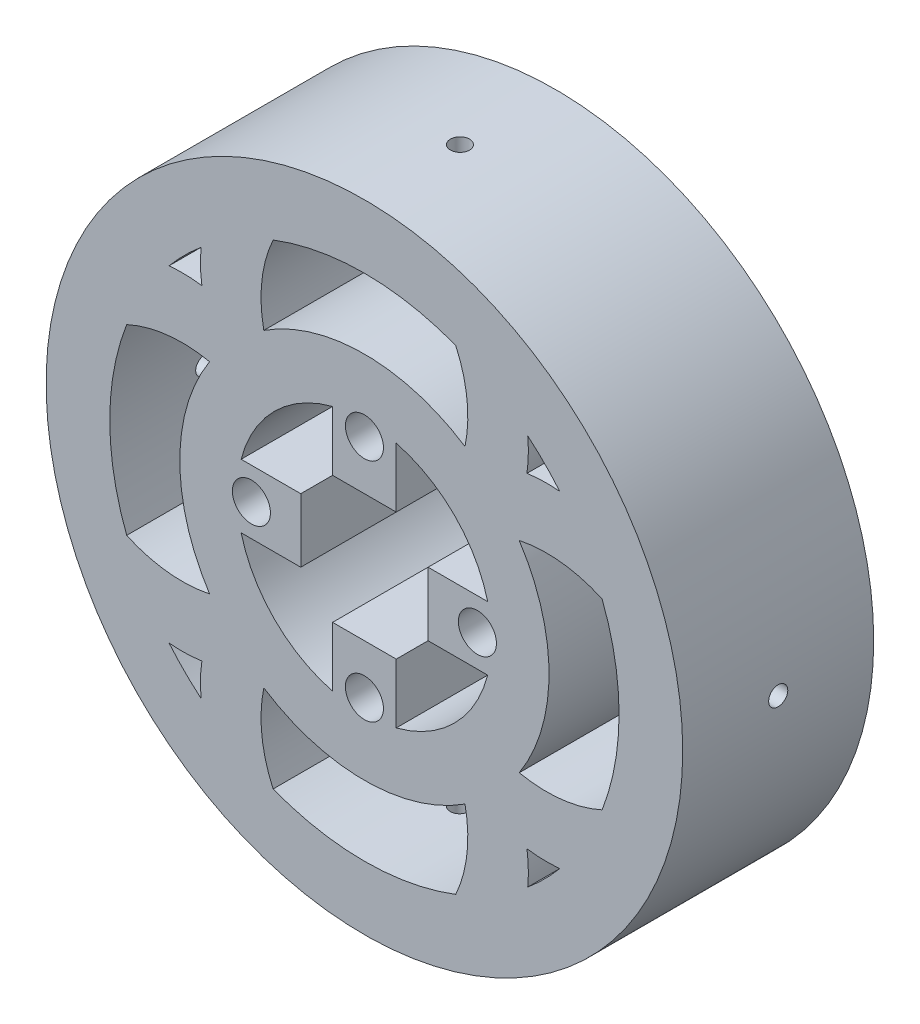
SolidWorks part; units mm, degrees
ref_plane "Front Plane" through (0, 0, 0) normal (0, 0, 1) x (1, 0, 0)
ref_plane "Top Plane" through (0, 0, 0) normal (0, 1, 0) x (1, 0, 0)
ref_plane "Right Plane" through (0, 0, 0) normal (1, 0, 0) x (0, 0, -1)
sketch "Sketch6" plane through (0, 0, 0) normal (0, 0, 1) x (1, 0, 0)
  circle A0 centre (0, 0) radius 20
  circle A1 centre (0, 0) radius 29
  dimension "D1" = 40
  dimension "D2" = 58
extrude "Inner Ring" add sketch "Sketch6" against normal blind 30 separate body
sketch "Sketch7" plane through (0, 0, 0) normal (0, 0, 1) x (1, 0, 0)
  line L2 (-10, 5) -> (-10, -5)
  line L3 (-5, 10) -> (5, 10)
  line L4 (10, 5) -> (10, -5)
  line L5 (-5, -10) -> (5, -10)
  line L14 (-19.3649, 5) -> (-10, 5)
  line L15 (-19.3649, -5) -> (-10, -5)
  line L16 (-5, 19.3649) -> (-5, 10)
  line L17 (5, 19.3649) -> (5, 10)
  line L18 (19.3649, 5) -> (10, 5)
  line L19 (19.3649, -5) -> (10, -5)
  line L20 (5, -19.3649) -> (5, -10)
  line L21 (-5, -19.3649) -> (-5, -10)
  circle A1 centre (0, 0) radius 20
  circle M19 centre (0, 0) radius 20
  dimension "D1" = 20
  dimension "D2" = 20
  dimension "D3" = 10
  dimension "D5" = 10
  dimension "D7" = 10
  dimension "D8" = 10
extrude "Motor Connector Cut" add sketch "Sketch7" against normal blind 30 contours L19 L18 L4 M19 | L17 L16 L3 M19 | L15 L2 L14 M19 | L21 L20 L5 M19
sketch "Sketch8" plane through (0, 0, 0) normal (0, 0, 1) x (1, 0, 0)
  circle A1 centre (0, 17.75) radius 2.987
  circle A2 centre (17.75, 0) radius 2.987
  circle A3 centre (0, -17.75) radius 2.987
  circle A4 centre (-17.75, 0) radius 2.987
  dimension "D1" = 5.974
  dimension "D2" = 5.974
  dimension "D3" = 5.974
  dimension "0.0049m" = 5.974
sketch "Sketch9" plane through (0, 0, 0) normal (0, 0, 1) x (1, 0, 0)
  circle A0 centre (0, 0) radius 50
  circle A18 centre (0, 0) radius 29
  dimension "D2" = 100
extrude "Outside Ring Extrusion" add sketch "Sketch9" against normal blind 30
sketch "Sketch12" plane through (0, 0, 0) normal (0, 0, 1) x (1, 0, 0)
  circle A0 centre (0, 0) radius 27.5
  circle A1 centre (0, 0) radius 45
  dimension "D1" = 55
  dimension "D2" = 90
extrude "Cut-Extrude6" cut sketch "Sketch12" against normal blind 56 and the other way blind 38
extrude "Motor Connector Holes" cut sketch "Sketch8" against normal blind 41 and the other way blind 27
sketch "Sketch10" plane through (0, 0, 0) normal (0, 0, 1) x (1, 0, 0)
  circle A0 centre (0, 0) radius 29
  arc A4 (-24.0947, 20.4191) -> (-41.6064, 16.7952) centre (-29, 0) ccw
  circle A5 centre (0, 0) radius 50
  arc A6 (-0.0957, 0) -> (0, 0.0957) centre (-17.7016, 17.7016) ccw
  arc A9 (-28.6072, 4.7568) -> (-42.4805, -14.6492) centre (-17.7016, -17.7016) ccw
  arc A10 (-20.4191, 24.0947) -> (-38.2638, 23.4049) centre (-28.6072, 4.7568) ccw
  arc A11 (-24.3176, 15.8004) -> (-43.8179, 9.722) centre (-28.6072, -4.7568) ccw
  circle A18 centre (0, 0) radius 29
  arc A19 (14.3758, 42.4453) -> (-4.7568, 28.6072) centre (17.7016, 17.7016) ccw
  circle A20 centre (0, -0.0957) radius 44.9043
  arc A21 (24.3176, -15.8004) -> (43.8731, -9.6638) centre (28.6072, 4.7568) ccw
  arc A22 (43.8179, 9.722) -> (24.3176, 15.8004) centre (28.6072, -4.7568) ccw
  arc A23 (41.6064, 16.7952) -> (21.3966, 19.5752) centre (29, 0) ccw
  arc A24 (49.5968, 4.0954) -> (49.3228, 8.2014) centre (28.6072, 4.7568) ccw
  arc A25 (49.5968, -4.0954) -> (49.5968, 4.0954) centre (29, 0) ccw
  arc A26 (28.6072, -4.7568) -> (42.4628, 14.5092) centre (17.7016, 17.7016) ccw
  arc A27 (42.4805, -14.6492) -> (28.6072, 4.7568) centre (17.7016, -17.7016) ccw
  arc A28 (49.3228, -8.2014) -> (49.5968, -4.0954) centre (28.6072, -4.7568) ccw
  arc A29 (25.5301, 25.5301) -> (23.4328, 38.2096) centre (4.7568, 28.6072) ccw
  arc A30 (23.2856, -38.4907) -> (22.8197, -17.8959) centre (4.7568, -28.6072) ccw
  arc A31 (20.4191, 24.0947) -> (16.8561, 41.5248) centre (0, 29) ccw
  arc A32 (24.0947, -20.4191) -> (41.717, -16.7116) centre (29, 0) ccw
  arc A33 (15.8004, 24.3176) -> (9.8231, 43.721) centre (-4.7568, 28.6072) ccw
  arc A34 (4.7568, 28.6072) -> (-14.3758, 42.4453) centre (-17.7016, 17.7016) ccw
  arc A35 (16.6483, -41.7998) -> (20.4191, -24.0947) centre (0, -29) ccw
  arc A36 (9.5599, -43.9706) -> (15.8004, -24.3176) centre (-4.7568, -28.6072) ccw
  arc A38 (17.8959, -22.8197) -> (38.435, -23.3152) centre (28.6072, -4.7568) ccw
  arc A39 (-14.7836, -42.4967) -> (4.7568, -28.6072) centre (-17.7016, -17.7016) ccw
  arc A40 (-38.435, -23.3152) -> (-20.4191, -24.0947) centre (-28.6072, -4.7568) ccw
  arc A41 (-43.8731, -9.6638) -> (-24.3176, -15.8004) centre (-28.6072, 4.7568) ccw
  arc A43 (-41.717, -16.7116) -> (-21.3966, -19.5752) centre (-29, 0) ccw
  arc A44 (0, -0.0957) -> (-0.0957, 0) centre (-17.7016, -17.7016) ccw
  arc A45 (-42.4628, 14.5092) -> (-28.6072, -4.7568) centre (-17.7016, 17.7016) ccw
  arc A46 (-4.7568, -28.6072) -> (14.7836, -42.4967) centre (17.7016, -17.7016) ccw
  arc A47 (-23.4328, 38.2096) -> (-24.0947, 20.4191) centre (-4.7568, 28.6072) ccw
  arc A48 (-15.8004, -24.3176) -> (-9.5599, -43.9706) centre (4.7568, -28.6072) ccw
  arc A49 (-16.8561, 41.5248) -> (-19.5752, 21.3966) centre (0, 29) ccw
  arc A50 (-20.4191, -24.0947) -> (-16.6483, -41.7998) centre (0, -29) ccw
  arc A51 (-9.8231, 43.721) -> (-15.8004, 24.3176) centre (4.7568, 28.6072) ccw
  arc A52 (-25.5301, -25.5301) -> (-23.2856, -38.4907) centre (-4.7568, -28.6072) ccw
  arc A53 (4.0954, 49.5968) -> (-4.0954, 49.5968) centre (0, 29) ccw
  arc A54 (8.2014, 49.3228) -> (0, 49.0614) centre (4.7568, 28.6072) ccw
  arc A55 (0, 49.0614) -> (-8.2014, 49.3228) centre (-4.7568, 28.6072) ccw
  arc A56 (38.2638, 23.4049) -> (25.5301, 25.5301) centre (28.6072, 4.7568) ccw
  circle A57 centre (-0.0957, 0) radius 27.4043
extrude "Pattern" add sketch "Sketch10" against normal blind 30
sketch "Sketch13" plane through (0, 0, 0) normal (0, 0, 1) x (1, 0, 0)
  circle A0 centre (0, 0) radius 45
  circle A2 centre (0, 0) radius 40
  dimension "D2" = 90
  dimension "D1" = 80
extrude "Boss-Extrude1" add sketch "Sketch13" against normal blind 30
ref_plane "Plane1" through (0, 50, 0) normal (0, 1, 0) x (1, 0, 0)
sketch "Sketch14" plane through (0, 50, 0) normal (0, 1, 0) x (1, 0, 0)
  line L0 (0, 0) -> (0, 30)
  circle A0 centre (0, 15) radius 1.5
  dimension "D1" = 30
extrude "Cut-Extrude7" cut sketch "Sketch14" against normal blind 13 contours L0 A0 | L0 A0
ref_plane "Plane2" through (0, -50, 0) normal (0, 1, 0) x (1, 0, 0)
sketch "Sketch15" plane through (0, -50, 0) normal (0, 1, 0) x (1, 0, 0)
  line L0 (0, 0) -> (0, 30)
  circle A0 centre (0, 15) radius 1.5
  dimension "D1" = 30
extrude "Cut-Extrude8" cut sketch "Sketch15" along normal blind 15 contours L0 A0 | L0 A0
ref_plane "Plane3" through (-50, 0, 0) normal (1, 0, 0) x (0, 0, -1)
sketch "Sketch16" plane through (-50, 0, 0) normal (1, 0, 0) x (0, 0, -1)
  line L0 (0, 0) -> (30, 0)
  line L1 (0, 50) -> (0, -50) construction
  line L2 (30, -50) -> (30, 50) construction
  circle A0 centre (15, 0) radius 1.5
extrude "Cut-Extrude9" cut sketch "Sketch16" along normal blind 17 contours L0 A0 | L0 A0
ref_plane "Plane4" through (50, 0, 0) normal (1, 0, 0) x (0, 0, -1)
sketch "Sketch17" plane through (50, 0, 0) normal (1, 0, 0) x (0, 0, -1)
  line L0 (0, 0) -> (30, 0)
  line L1 (0, 50) -> (0, -50) construction
  line L2 (30, -50) -> (30, 50) construction
  circle A0 centre (15, 0) radius 1.5
extrude "Cut-Extrude10" cut sketch "Sketch17" against normal blind 17 contours L0 A0 | L0 A0
